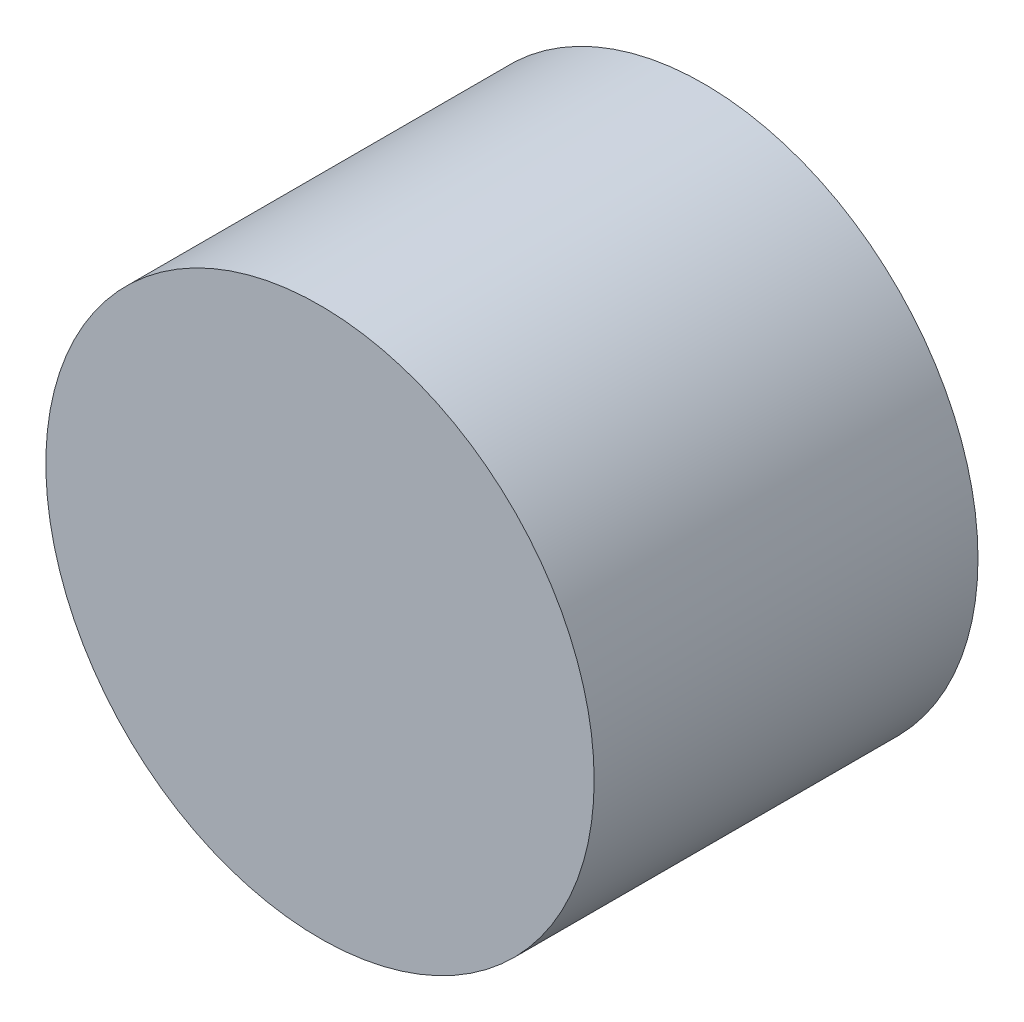
SolidWorks part; units mm, degrees
ref_plane "Front Plane" through (0, 0, 0) normal (0, 0, 1) x (1, 0, 0)
ref_plane "Top Plane" through (0, 0, 0) normal (0, 1, 0) x (1, 0, 0)
ref_plane "Right Plane" through (0, 0, 0) normal (1, 0, 0) x (0, 0, -1)
sketch "Sketch1" plane through (0, 0, 0) normal (0, 0, 1) x (1, 0, 0)
  circle A0 centre (0, 0) radius 2.5
  dimension "D1" = 5
extrude "Boss-Extrude1" add sketch "Sketch1" along normal blind 3.5
